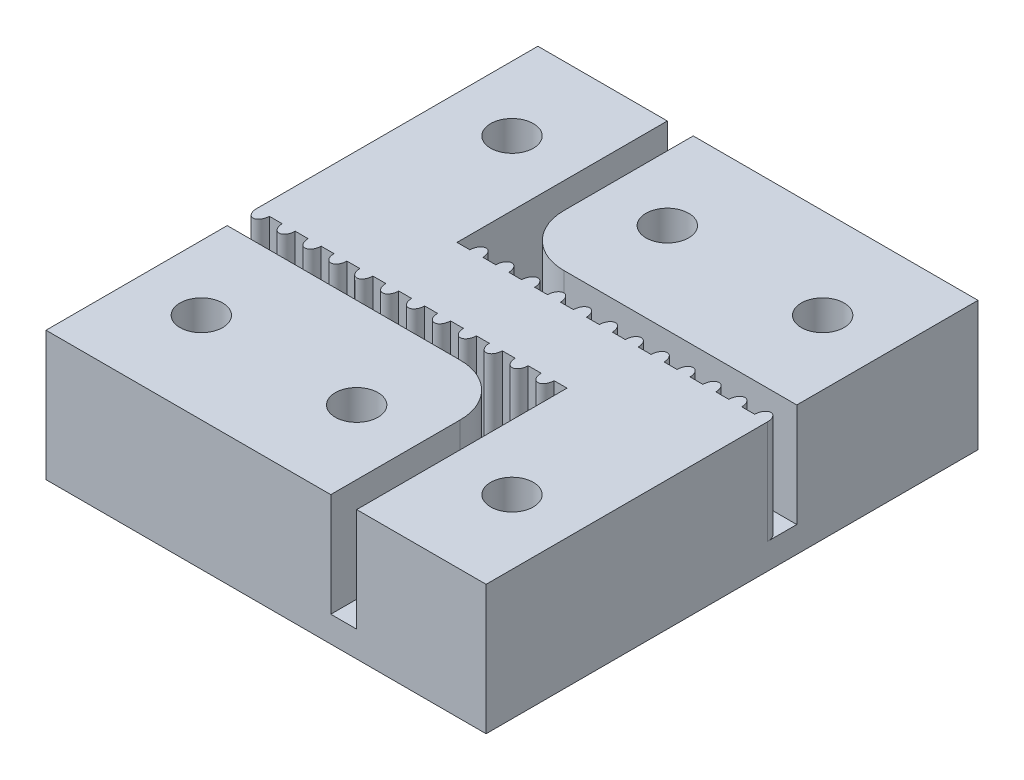
SolidWorks part; units mm, degrees
ref_plane "前视基准面" through (0, 0, 0) normal (0, 0, 1) x (1, 0, 0)
ref_plane "上视基准面" through (0, 0, 0) normal (0, 1, 0) x (1, 0, 0)
ref_plane "右视基准面" through (0, 0, 0) normal (1, 0, 0) x (0, 0, -1)
sketch "草图1" plane through (0, 0, 0) normal (0, 1, 0) x (1, 0, 0)
  line L0 (0, 0) -> (34, 0)
  line L1 (34, 0) -> (34, 38)
  line L2 (34, 38) -> (0, 38)
  line L3 (0, 38) -> (0, 0)
  dimension "D1" = 34
  dimension "D2" = 38
extrude "凸台-拉伸1" add sketch "草图1" along normal blind 10
sketch "草图2" plane through (0, 10, 0) normal (0, 1, 0) x (1, 0, 0)
  line L0 (0, 38) -> (0, 0) construction
  line L2 (0, 0) -> (34, 0) construction
  circle A0 centre (5, 7) radius 1.65
  circle A3 centre (17, 7) radius 1.65
  circle A4 centre (29, 7) radius 1.65
  circle A5 centre (17, 31) radius 1.65
  circle A6 centre (29, 31) radius 1.65
  circle A7 centre (5, 31) radius 1.65
  dimension "D1" = 3.3
  dimension "D2" = 3
  dimension "D3" = 2
  dimension "D4" = 5
  dimension "D7" = 7
extrude "切除-拉伸1" cut sketch "草图2" against normal through all
sketch "草图3" plane through (0, 10, 0) normal (0, 1, 0) x (1, 0, 0)
  line L0 (0, 14) -> (22, 14)
  line L1 (0, 38) -> (0, 0) construction
  line L2 (22, 14) -> (22, 0)
  line L3 (0, 0) -> (34, 0) construction
  line L13 (22, 0) -> (24, 0)
  line L37 (0, 16.25) -> (0, 14)
  line L38 (-12.5618, 19) -> (49.5347, 19) construction
  line L39 (17, -8.6981) -> (17, 25.9508) construction
  line L57 (1, 16.25) -> (2, 16.25)
  line L64 (3, 16.25) -> (4, 16.25)
  line L77 (24, 0) -> (24, 16.25)
  line L93 (10, 38) -> (10, 21.75) [skipped]
  line L94 (31, 21.75) -> (30, 21.75) [skipped]
  line L95 (33, 21.75) -> (32, 21.75) [skipped]
  line L96 (34, 21.75) -> (34, 24) [skipped]
  line L97 (34, 24) -> (12, 24) [skipped]
  line L98 (12, 24) -> (12, 38) [skipped]
  line L99 (12, 38) -> (10, 38) [skipped]
  line L100 (5, 16.25) -> (6, 16.25)
  line L101 (7, 16.25) -> (8, 16.25)
  line L102 (9, 16.25) -> (10, 16.25)
  line L103 (11, 16.25) -> (12, 16.25)
  line L104 (13, 16.25) -> (14, 16.25)
  line L105 (15, 16.25) -> (16, 16.25)
  line L106 (17, 16.25) -> (18, 16.25)
  line L107 (19, 16.25) -> (20, 16.25)
  line L108 (21, 16.25) -> (22, 16.25)
  line L109 (23, 16.25) -> (24, 16.25)
  line L110 (34, 24) -> (12, 24)
  line L111 (12, 24) -> (12, 38)
  line L112 (12, 38) -> (10, 38)
  line L113 (10, 38) -> (10, 21.75)
  line L114 (11, 21.75) -> (10, 21.75)
  line L115 (13, 21.75) -> (12, 21.75)
  line L116 (15, 21.75) -> (14, 21.75)
  line L117 (17, 21.75) -> (16, 21.75)
  line L118 (19, 21.75) -> (18, 21.75)
  line L119 (21, 21.75) -> (20, 21.75)
  line L120 (23, 21.75) -> (22, 21.75)
  line L121 (25, 21.75) -> (24, 21.75)
  line L122 (27, 21.75) -> (26, 21.75)
  line L123 (29, 21.75) -> (28, 21.75)
  line L124 (31, 21.75) -> (30, 21.75)
  line L125 (33, 21.75) -> (32, 21.75)
  line L126 (34, 21.75) -> (34, 24)
  ellipse E0 centre (0.5, 16.25) end of major axis (0.5, 17) minor radius 0.5 (0, 16.25) -> (1, 16.25) ccw
  ellipse E1 centre (2.5, 16.25) end of major axis (2.5, 15.5) minor radius 0.5 (2, 16.25) -> (3, 16.25) ccw
  ellipse E2 centre (4.5, 16.25) end of major axis (4.5, 17) minor radius 0.5 (4, 16.25) -> (5, 16.25) ccw
  ellipse E3 centre (6.5, 16.25) end of major axis (6.5, 15.5) minor radius 0.5 (6, 16.25) -> (7, 16.25) ccw
  ellipse E4 centre (8.5, 16.25) end of major axis (8.5, 17) minor radius 0.5 (8, 16.25) -> (9, 16.25) ccw
  ellipse E5 centre (10.5, 16.25) end of major axis (10.5, 15.5) minor radius 0.5 (10, 16.25) -> (11, 16.25) ccw
  ellipse E6 centre (12.5, 16.25) end of major axis (12.5, 17) minor radius 0.5 (12, 16.25) -> (13, 16.25) ccw
  ellipse E7 centre (14.5, 16.25) end of major axis (14.5, 15.5) minor radius 0.5 (14, 16.25) -> (15, 16.25) ccw
  ellipse E8 centre (16.5, 16.25) end of major axis (16.5, 17) minor radius 0.5 (16, 16.25) -> (17, 16.25) ccw
  ellipse E9 centre (18.5, 16.25) end of major axis (18.5, 15.5) minor radius 0.5 (18, 16.25) -> (19, 16.25) ccw
  ellipse E10 centre (20.5, 16.25) end of major axis (20.5, 17) minor radius 0.5 (20, 16.25) -> (21, 16.25) ccw
  ellipse E11 centre (22.5, 16.25) end of major axis (22.5, 15.5) minor radius 0.5 (22, 16.25) -> (23, 16.25) ccw
  ellipse E12 centre (11.5, 21.75) end of major axis (11.5, 22.5) minor radius 0.5 (12, 21.75) -> (11, 21.75) ccw
  ellipse E13 centre (13.5, 21.75) end of major axis (13.5, 22.5) minor radius 0.5 (14, 21.75) -> (13, 21.75) ccw
  ellipse E14 centre (15.5, 21.75) end of major axis (15.5, 22.5) minor radius 0.5 (16, 21.75) -> (15, 21.75) ccw
  ellipse E15 centre (17.5, 21.75) end of major axis (17.5, 21) minor radius 0.5 (18, 21.75) -> (17, 21.75) ccw
  ellipse E16 centre (19.5, 21.75) end of major axis (19.5, 22.5) minor radius 0.5 (20, 21.75) -> (19, 21.75) ccw
  ellipse E17 centre (21.5, 21.75) end of major axis (21.5, 21) minor radius 0.5 (22, 21.75) -> (21, 21.75) ccw
  ellipse E18 centre (23.5, 21.75) end of major axis (23.5, 22.5) minor radius 0.5 (24, 21.75) -> (23, 21.75) ccw
  ellipse E19 centre (25.5, 21.75) end of major axis (25.5, 21) minor radius 0.5 (26, 21.75) -> (25, 21.75) ccw
  ellipse E20 centre (27.5, 21.75) end of major axis (27.5, 22.5) minor radius 0.5 (28, 21.75) -> (27, 21.75) ccw
  ellipse E21 centre (29.5, 21.75) end of major axis (29.5, 21) minor radius 0.5 (30, 21.75) -> (29, 21.75) ccw
  ellipse E22 centre (31.5, 21.75) end of major axis (31.5, 22.5) minor radius 0.5 (32, 21.75) -> (31, 21.75) ccw
  ellipse E23 centre (33.5, 21.75) end of major axis (33.5, 21) minor radius 0.5 (34, 21.75) -> (33, 21.75) ccw
  point P8 (17, 19)
  point P63 (17, 19)
  point P191 (17, 19)
  point P275 (17, 19)
  dimension "D5" = 0.5
  dimension "D8" = 0.5
  dimension "D2" = 14
  dimension "D3" = 22
  dimension "D4" = 19
  dimension "D6" = 2
  dimension "D7" = 17
  dimension "D9" = 2
  dimension "D10" = 1
  dimension "D11" = 1.5
  dimension "D12" = 2
  dimension "D13" = 0.75
  dimension "D14" = 6
  dimension "D15" = 2
extrude "切除-拉伸2" cut sketch "草图3" against normal blind 8
fillet "圆角1" radius 4 2 edges at (22, 6, -14) (12, 6, -24)
sketch "草图4" plane through (0, 0, 0) normal (0, -1, 0) x (1, 0, 0)
  circle A0 centre (5, -7) radius 2.9
  circle A1 centre (17, -7) radius 2.9
  circle A2 centre (29, -7) radius 2.9
  circle A3 centre (17, -31) radius 2.9
  circle A4 centre (29, -31) radius 2.9
  circle A5 centre (5, -31) radius 2.9
  dimension "D1" = 5.8
  dimension "D2" = 3
  dimension "D3" = 2
extrude "切除-拉伸3" cut sketch "草图4" against normal blind 3.2
